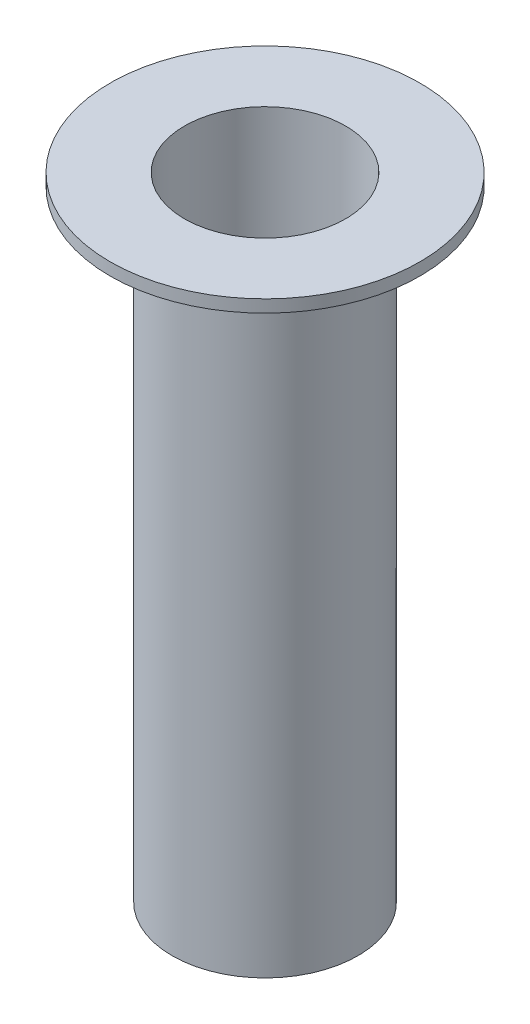
SolidWorks part; units mm, degrees
ref_plane "Front Plane" through (0, 0, 0) normal (0, 0, 1) x (1, 0, 0)
ref_plane "Top Plane" through (0, 0, 0) normal (0, 1, 0) x (1, 0, 0)
ref_plane "Right Plane" through (0, 0, 0) normal (1, 0, 0) x (0, 0, -1)
sketch "Sketch1" plane through (0, 0, 0) normal (0, 1, 0) x (1, 0, 0)
  circle A0 centre (0, 0) radius 5.2
  circle A2 centre (0, 0) radius 6
  dimension "D1" = 10.4
  dimension "D2" = 0.8
extrude "Boss-Extrude1" add sketch "Sketch1" along normal mid plane 40
sketch "Sketch4" plane through (0, 20, 0) normal (0, 1, 0) x (1, 0, 0)
  circle A0 centre (0, 0) radius 5.2
  circle A1 centre (0, 0) radius 10
  dimension "D1" = 20
extrude "Boss-Extrude3" add sketch "Sketch4" along normal blind 0.8
